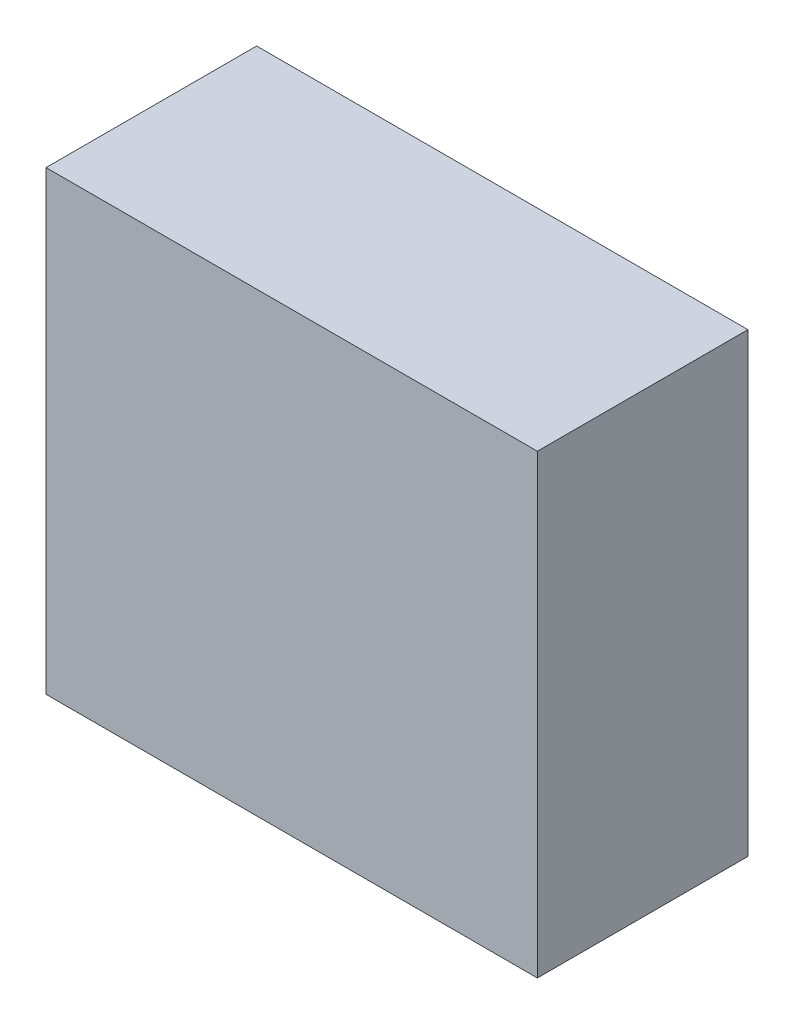
SolidWorks part; units mm, degrees
material "Pure Lead"
ref_plane "Front Plane" through (0, 0, 0) normal (0, 0, 1) x (1, 0, 0)
ref_plane "Top Plane" through (0, 0, 0) normal (0, 1, 0) x (1, 0, 0)
ref_plane "Right Plane" through (0, 0, 0) normal (1, 0, 0) x (0, 0, -1)
sketch "Sketch1" plane through (0, 0, 0) normal (0, 1, 0) x (1, 0, 0)
  line L1 (0, 0) -> (177.8, 0)
  line L2 (0, 0) -> (0, 76.2)
  line L3 (0, 76.2) -> (177.8, 76.2)
  line L4 (177.8, 0) -> (177.8, 76.2)
  dimension "D1" = 76.2
  dimension "D2" = 177.8
extrude "Boss-Extrude1" add sketch "Sketch1" along normal blind 165.1
